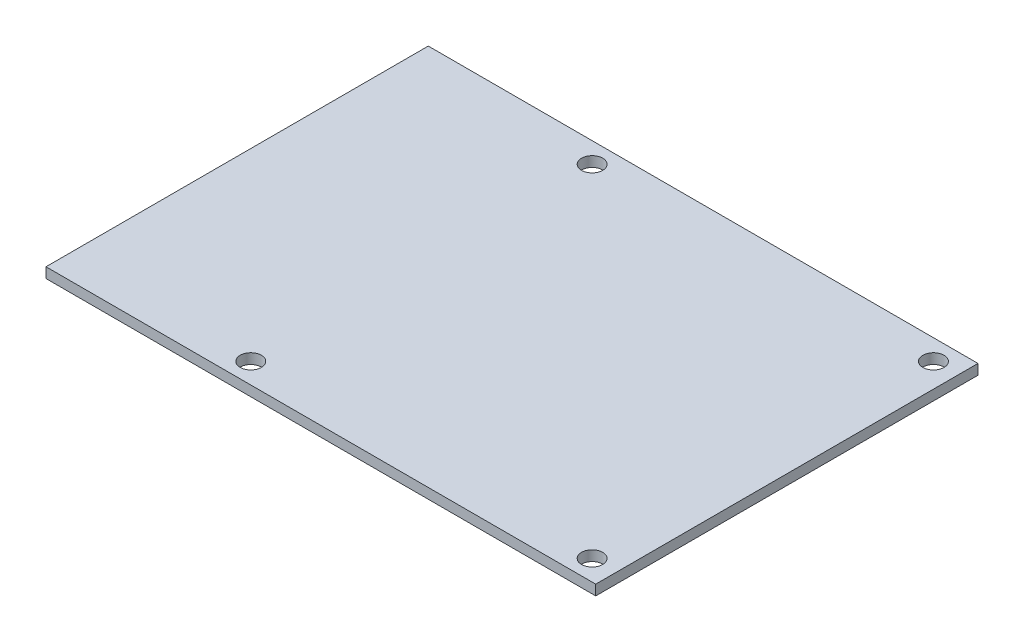
SolidWorks part; units mm, degrees
ref_plane "前视基准面" through (0, 0, 0) normal (0, 0, 1) x (1, 0, 0)
ref_plane "上视基准面" through (0, 0, 0) normal (0, 1, 0) x (1, 0, 0)
ref_plane "右视基准面" through (0, 0, 0) normal (1, 0, 0) x (0, 0, -1)
other "Configuration Table"
sketch "草图1" plane through (0, 0, 0) normal (0, 1, 0) x (1, 0, 0)
  line L1 (44, -28) -> (-36.527, -28)
  line L2 (44, -28) -> (44, 28)
  line L3 (44, 28) -> (-36.527, 28)
  line L4 (-36.527, -28) -> (-36.527, 28)
  circle A0 centre (-9.527, 25) radius 1.55
  circle A1 centre (-9.527, -25) radius 1.55
  circle A2 centre (40.473, -25) radius 1.55
  circle A3 centre (40.473, 25) radius 1.55
  point P0 (0, 0)
  point P14 (0, 0)
  point P15 (0, 0)
  point P16 (0, 0)
  point P17 (0, 0)
  point P18 (0, 0)
  dimension "D3" = 3.1
  dimension "D4" = 3.1
  dimension "D5" = 3.1
  dimension "D6" = 3.1
  dimension "D1" = 28
  dimension "D2" = 27
  dimension "D7" = 25
  dimension "D8" = 25
  dimension "D9" = 50
  dimension "D10" = 28
  dimension "D11" = 44
  dimension "D12" = 3.527
extrude "凸台-拉伸1" add sketch "草图1" along normal blind 1.5
